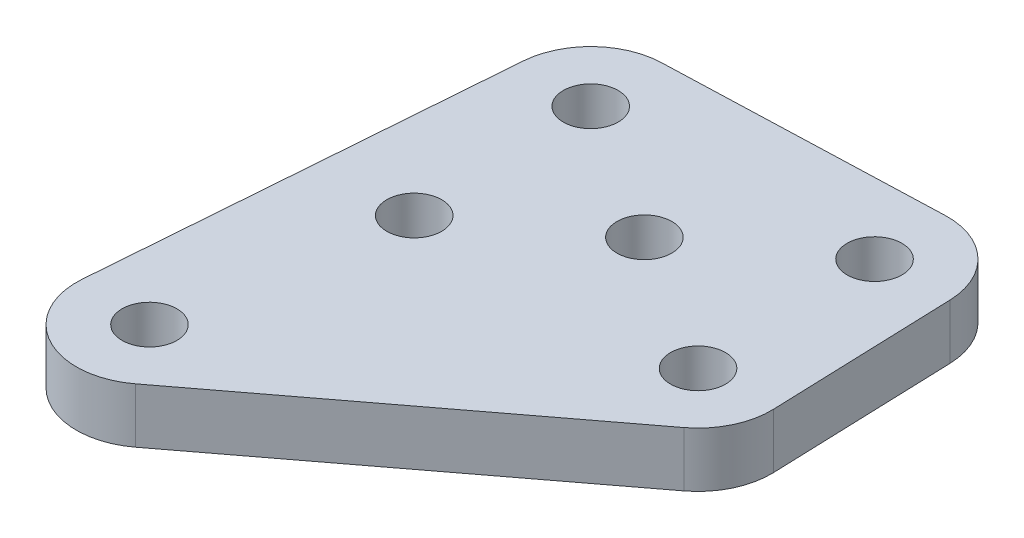
SolidWorks part; units mm, degrees
ref_plane "Front Plane" through (0, 0, 0) normal (0, 0, 1) x (1, 0, 0)
ref_plane "Top Plane" through (0, 0, 0) normal (0, 1, 0) x (1, 0, 0)
ref_plane "Right Plane" through (0, 0, 0) normal (1, 0, 0) x (0, 0, -1)
sketch "Sketch1" plane through (0, 0, 0) normal (0, 1, 0) x (1, 0, 0)
  line L21 (-21.2204, -4.8402) -> (-38.2818, -17.7612)
  line L22 (-19.9851, 8.4815) -> (-19.6377, -1.5125)
  line L23 (-39.1126, 11.8191) -> (-24.1216, 12.3401)
  line L24 (-44.6849, -14.2655) -> (-42.9618, 8.1284)
  circle A49 centre (-23.6353, -1.6514) radius 1.5
  circle A50 centre (-31.3044, 3.085) radius 1.5
  circle A51 centre (-23.9827, 8.3426) radius 1.5
  circle A52 centre (-38.9736, 7.8215) radius 1.5
  circle A53 centre (-38.6262, -2.1725) radius 1.5
  circle A54 centre (-40.6967, -14.5724) radius 1.5
  arc A55 (-38.2818, -17.7612) -> (-44.6849, -14.2655) centre (-40.6967, -14.5724) cw
  arc A56 (-19.6377, -1.5125) -> (-21.2204, -4.8402) centre (-23.6353, -1.6514) cw
  arc A57 (-24.1216, 12.3401) -> (-19.9851, 8.4815) centre (-23.9827, 8.3426) cw
  arc A58 (-42.9618, 8.1284) -> (-39.1126, 11.8191) centre (-38.9736, 7.8215) cw
extrude "Boss-Extrude1" add sketch "Sketch1" along normal blind 3
